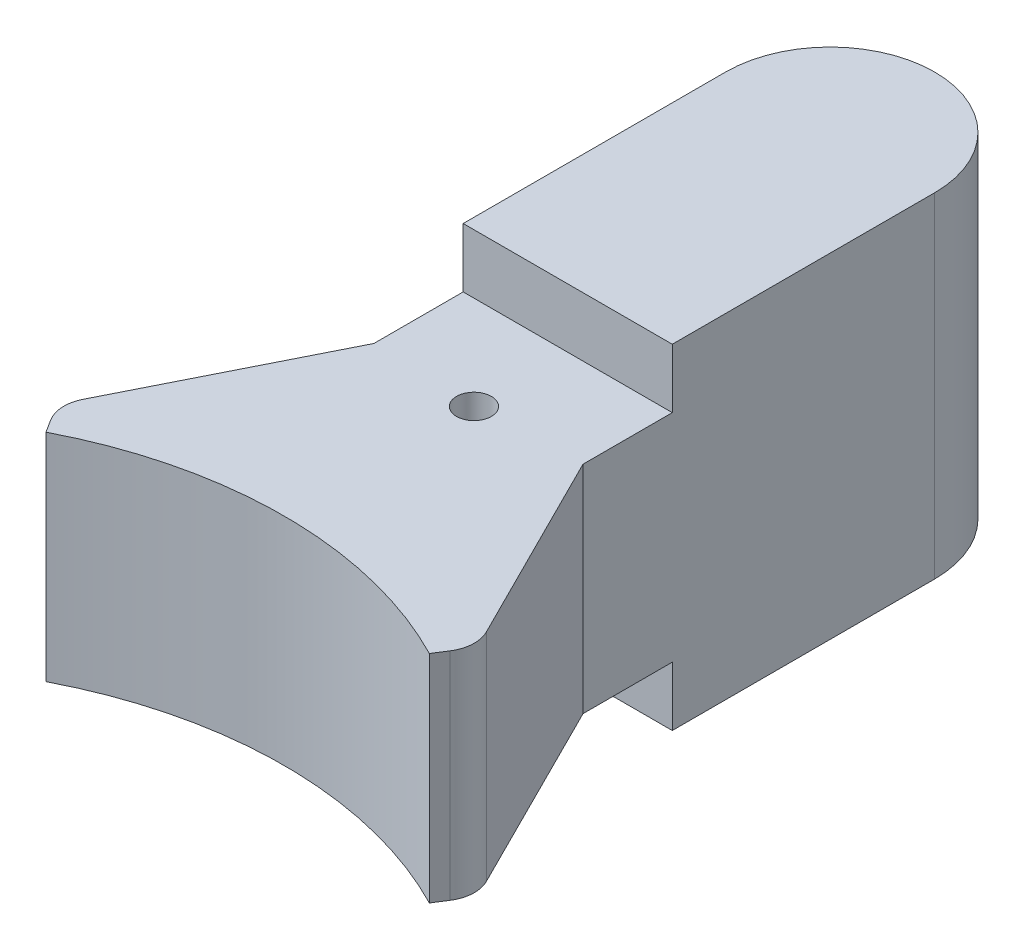
SolidWorks part; units mm, degrees
ref_plane "Front Plane" through (0, 0, 0) normal (0, 0, 1) x (1, 0, 0)
ref_plane "Top Plane" through (0, 0, 0) normal (0, 1, 0) x (1, 0, 0)
ref_plane "Right Plane" through (0, 0, 0) normal (1, 0, 0) x (0, 0, -1)
sketch "Sketch1" plane through (0, 0, 0) normal (0, 1, 0) x (1, 0, 0)
  line L0 (-3, -1.0913) -> (-3, 9)
  line L5 (3, -1.0913) -> (3, 9)
  line L7 (-5.5, -8) -> (-5.7327, -7.6347)
  line L8 (-5.7835, -6.6497) -> (-3, -1.0913)
  line L10 (5.5, -8) -> (5.7327, -7.6347)
  line L11 (5.7835, -6.6497) -> (3, -1.0913)
  line L12 (0, 0) -> (0, 3.0536) construction
  circle A1 centre (0, 9) radius 3
  circle A2 centre (0, -1.22) radius 0.5
  arc A3 (-5.5, -8) -> (5.5, -8) centre (0, -18.6654) cw
  arc A4 (5.7327, -7.6347) -> (5.7835, -6.6497) centre (4.8893, -7.0974) ccw
  arc A5 (-5.7327, -7.6347) -> (-5.7835, -6.6497) centre (-4.8893, -7.0974) cw
  point P22 (-6.0373, -7.1566)
  dimension "D1" = 6
  dimension "D2" = 1
  dimension "D5" = 12
  dimension "D6" = 1
  dimension "D3" = 1
  dimension "D4" = 8
  dimension "D7" = 65
  dimension "D8" = 11
  dimension "D9" = 1.22
  dimension "D10" = 9
  dimension "D11" = 53.2
extrude "Boss-Extrude1" add sketch "Sketch1" along normal mid plane 9.6
sketch "Sketch3" plane through (0, 0, 0) normal (1, 0, 0) x (0, 0, -1)
  line L0 (0, 0) -> (-12.4642, 0) construction
  line L1 (1.4707, 6.1487) -> (-10.2496, 6.1487)
  line L2 (1.4707, 6.1487) -> (1.4707, 3.1)
  line L3 (1.4707, 3.1) -> (-10.2496, 3.1)
  line L4 (-10.2496, 6.1487) -> (-10.2496, 3.1)
  line L5 (1.4707, -6.9396) -> (-9.8181, -6.9396)
  line L6 (1.4707, -6.9396) -> (1.4707, -3.1)
  line L7 (1.4707, -3.1) -> (-9.8181, -3.1)
  line L8 (-9.8181, -6.9396) -> (-9.8181, -3.1)
  dimension "D1" = 6.2
extrude "Cut-Extrude1" cut sketch "Sketch3" against normal through all both and the other way through all
